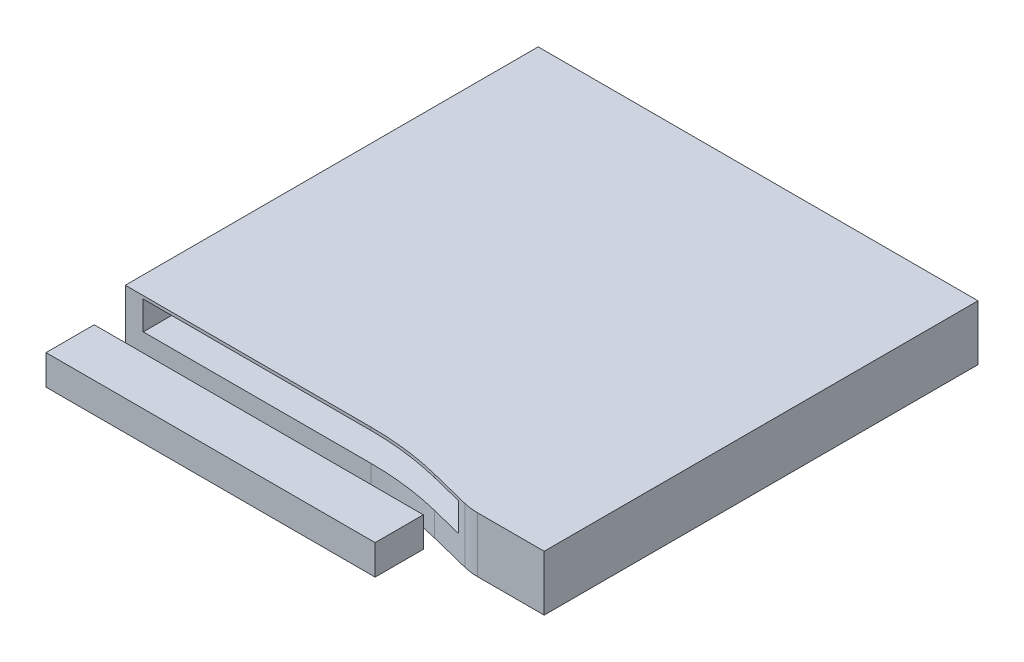
SolidWorks part; units mm, degrees
ref_plane "前视基准面" through (0, 0, 0) normal (0, 0, 1) x (1, 0, 0)
ref_plane "上视基准面" through (0, 0, 0) normal (0, 1, 0) x (1, 0, 0)
ref_plane "右视基准面" through (0, 0, 0) normal (1, 0, 0) x (0, 0, -1)
sketch "草图1" plane through (0, 0, 0) normal (0, 1, 0) x (1, 0, 0)
  line L0 (0, -13.8) -> (8.2067, -13.8)
  line L1 (0, 0) -> (14.7, 0)
  line L3 (0, -14.5) -> (12.2325, -14.5) construction
  line L4 (14.7, 0) -> (14.7, -14.5)
  line L5 (10.6396, -14.1005) -> (11.9929, -14.4399)
  line L6 (12.4795, -14.5) -> (14.7, -14.5)
  line L7 (0, 0) -> (0, -13.8)
  line L8 (0, -13.8) -> (0, -14.5) construction
  arc A0 (10.6396, -14.1005) -> (8.2067, -13.8) centre (8.2067, -23.8) ccw
  arc A1 (11.9929, -14.4399) -> (12.4795, -14.5) centre (12.4795, -12.5) ccw
  dimension "D4" = 10
  dimension "D5" = 2
  dimension "D1" = 14.7
  dimension "D2" = 14.5
  dimension "D3" = 13.8
extrude "凸台-拉伸1" add sketch "草图1" along normal blind 1.85
sketch "草图2" plane through (0, 0, 0) normal (0, -1, 0) x (1, 0, 0)
  line L0 (14.7, 0) -> (0, 0) construction
  line L1 (7.35, 14.5) -> (7.35, 0) construction
  line L3 (14.7, 0) -> (0, 0) construction
  circle A0 centre (2.4, 10.5) radius 0.4
  circle A1 centre (10.4, 10.5) radius 0.4
  point P12 (7.35, 0)
  dimension "D2" = 0.8
  dimension "D1" = 10.5
  dimension "D3" = 8
  dimension "D4" = 3.05
extrude "凸台-拉伸2" add sketch "草图2" along normal blind 0.59
sketch "草图3" plane through (0, 0, 0) normal (0, 0, -1) x (-1, 0, 0)
  line L0 (-14.7, 0) -> (0, 0) construction
  line L2 (-9.75, 0) -> (-9.45, 0)
  line L3 (-9.75, 0) -> (-9.75, 0.1)
  line L4 (-9.75, 0.1) -> (-9.45, 0.1)
  line L5 (-9.45, 0) -> (-9.45, 0.1)
  line L33 (-8.65, 0) -> (-8.65, 0.1)
  line L34 (-8.65, 0) -> (-8.35, 0)
  line L35 (-8.35, 0) -> (-8.35, 0.1)
  line L36 (-8.65, 0.1) -> (-8.35, 0.1)
  line L37 (-7.55, 0) -> (-7.55, 0.1)
  line L38 (-7.55, 0) -> (-7.25, 0)
  line L39 (-7.25, 0) -> (-7.25, 0.1)
  line L40 (-7.55, 0.1) -> (-7.25, 0.1)
  line L41 (-6.45, 0) -> (-6.45, 0.1)
  line L42 (-6.45, 0) -> (-6.15, 0)
  line L43 (-6.15, 0) -> (-6.15, 0.1)
  line L44 (-6.45, 0.1) -> (-6.15, 0.1)
  line L45 (-5.35, 0) -> (-5.35, 0.1)
  line L46 (-5.35, 0) -> (-5.05, 0)
  line L47 (-5.05, 0) -> (-5.05, 0.1)
  line L48 (-5.35, 0.1) -> (-5.05, 0.1)
  line L49 (-4.25, 0) -> (-4.25, 0.1)
  line L50 (-4.25, 0) -> (-3.95, 0)
  line L51 (-3.95, 0) -> (-3.95, 0.1)
  line L52 (-4.25, 0.1) -> (-3.95, 0.1)
  line L53 (-3.15, 0) -> (-3.15, 0.1)
  line L54 (-3.15, 0) -> (-2.85, 0)
  line L55 (-2.85, 0) -> (-2.85, 0.1)
  line L56 (-3.15, 0.1) -> (-2.85, 0.1)
  line L57 (-2.05, 0) -> (-2.05, 0.1)
  line L58 (-2.05, 0) -> (-1.75, 0)
  line L59 (-1.75, 0) -> (-1.75, 0.1)
  line L60 (-2.05, 0.1) -> (-1.75, 0.1)
  line L61 (-0.95, 0) -> (-0.95, 0.1)
  line L62 (-0.95, 0) -> (-0.65, 0)
  line L63 (-0.65, 0) -> (-0.65, 0.1)
  line L64 (-0.95, 0.1) -> (-0.65, 0.1)
  line L65 (-9.75, 0) -> (-8.65, 0) construction
  point P6 (-9.6, 0)
  dimension "D1" = 0.1
  dimension "D2" = 0.3
  dimension "D4" = 5.1
  dimension "D5" = 1.1
  dimension "D3" = 9
extrude "凸台-拉伸3" add sketch "草图3" along normal blind 0.5 separate body
sketch "草图4" plane through (0, 0, 14.5) normal (0, 0, 1) x (1, 0, 0)
  line L0 (0, 1.85) -> (8.2067, 1.85) construction
  line L1 (0.6, 1.75) -> (11.7, 1.75)
  line L2 (0.6, 1.75) -> (0.6, 0.8)
  line L3 (0.6, 0.8) -> (11.7, 0.8)
  line L4 (11.7, 1.75) -> (11.7, 0.8)
  line L5 (14.7, 1.85) -> (14.7, 0) construction
  dimension "D1" = 0.95
  dimension "D2" = 11.1
  dimension "D3" = 0.1
  dimension "D4" = 3
extrude "切除-拉伸1" cut sketch "草图4" against normal blind 14
ref_plane "基准面1" through (0, 1.275, 0) normal (0, -1, 0) x (-1, 0, 0)
sketch "草图5" plane through (0, 1.85, 0) normal (0, 1, 0) x (1, 0, 0)
  line L0 (0.65, -17.1) -> (11.65, -17.1) construction
  line L1 (14.7, 0) -> (0, 0) construction
  line L2 (11.7, -0.5) -> (0.6, -0.5) construction
  line L4 (0.65, -17.1) -> (11.65, -17.1)
  line L5 (0.65, -17.1) -> (0.65, -15.4889)
  line L6 (0.65, -15.4889) -> (11.65, -15.4889)
  line L7 (11.65, -17.1) -> (11.65, -15.4889)
  point P8 (6.15, -0.5)
  point P9 (6.15, -17.1)
  dimension "D1" = 17.1
  dimension "D2" = 11
extrude "凸台-拉伸4" add sketch "草图5" against normal blind 0.4 and the other way blind 0.6 from surface at -0.575 separate body starting at plane "基准面1"
ref_plane "卡中心轴" through (6.15, 0, 0) normal (-1, 0, 0) x (0, 0, 1)
